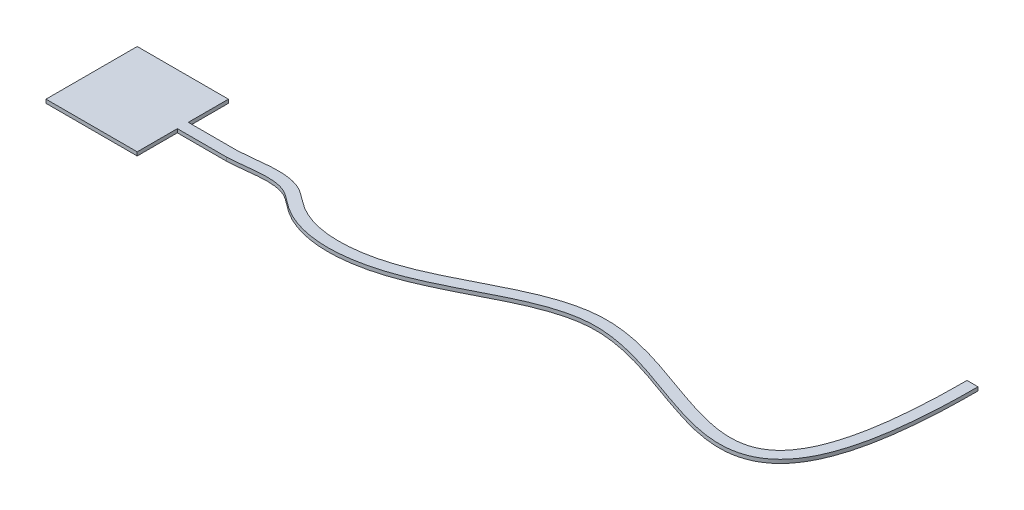
SolidWorks part; units mm, degrees
ref_plane "Front Plane" through (0, 0, 0) normal (0, 0, 1) x (1, 0, 0)
ref_plane "Top Plane" through (0, 0, 0) normal (0, 1, 0) x (1, 0, 0)
ref_plane "Right Plane" through (0, 0, 0) normal (1, 0, 0) x (0, 0, -1)
sketch "Sketch1" plane through (0, 0, 0) normal (0, 1, 0) x (1, 0, 0)
  line L1 (-159.8639, 116.4966) -> (90.1361, 116.4966)
  line L2 (-159.8639, 116.4966) -> (-159.8639, -133.5034)
  line L3 (-159.8639, -133.5034) -> (90.1361, -133.5034)
  line L4 (90.1361, 116.4966) -> (90.1361, -133.5034)
  dimension "D1" = 250
  dimension "D2" = 250
extrude "Boss-Extrude1" add sketch "Sketch1" along normal blind 10
sketch "Sketch2" plane through (0, 10, 0) normal (0, 1, 0) x (1, 0, 0)
  line L0 (90.1361, 116.4966) -> (-159.8639, -133.5034) construction
  line L1 (-159.8639, 116.4966) -> (-159.8639, -133.5034) construction
  line L2 (-159.8639, 116.4966) -> (90.1361, -133.5034) construction
  line L3 (90.1361, 6.4966) -> (90.1361, -23.5034)
  line L4 (1785.1361, 461.0452) -> (1800.1361, 461.0452)
  line L8 (90.1361, -23.5034) -> (224.5985, -23.5034)
  line L9 (90.1361, 6.4966) -> (224.0514, 6.4966)
  line L10 (1785.1361, 461.0452) -> (1770.1361, 461.0452)
  spline S2 degree 3 poles (224.5985, -23.5034) (224.908, -23.4922) (225.5226, -23.4698) (226.7878, -23.419) (228.9875, -23.3209) (233.4066, -23.0851) (242.2645, -22.4728) (254.982, -21.2788) (270.2563, -19.5904) (290.5175, -17.3215) (315.389, -15.0436) (338.8326, -14.9892) (356.2104, -17.0291) (368.4432, -19.7435) (377.9563, -23.1246) (385.0989, -26.5469) (392.1865, -30.6076) (401.3147, -36.9117) (412.7469, -45.7442) (422.9089, -53.527) (431.6523, -59.5736) (440.5529, -65.2298) (452.001, -71.6499) (470.9075, -80.5498) (495.5123, -89.2063) (526.1719, -95.9551) (557.5929, -99.3879) (589.4283, -99.8152) (631.9947, -96.7756) (684.568, -86.9) (744.2911, -67.568) (801.3603, -43.1962) (856.3224, -16.1061) (909.7596, 11.4274) (962.1896, 37.174) (1014.079, 58.9505) (1057.2245, 72.0427) (1091.9375, 78.5028) (1113.7809, 80.6772) (1131.4106, 81.1724) (1149.2625, 80.8598) (1171.9253, 79.0433) (1199.6038, 74.8439) (1237.0165, 66.9225) (1284.4839, 53.3806) (1341.7849, 33.6899) (1398.7165, 13.0067) (1454.6542, -6.195) (1509.0784, -21.408) (1561.5995, -30.0255) (1611.9257, -29.1774) (1651.4323, -17.73) (1680.5206, -0.6421) (1707.5138, 21.9705) (1730.9359, 53.0903) (1750.6053, 93.3966) (1763.5069, 128.508) (1774.5489, 168.8086) (1782.1817, 206.9939) (1787.3253, 240.4712) (1790.695, 267.0859) (1793.5695, 295.2491) (1795.9411, 325.0026) (1797.4914, 351.1569) (1798.4717, 372.917) (1799.0758, 389.6603) (1799.5478, 406.8328) (1799.8863, 424.4363) (1800.0564, 439.4798) (1800.1247, 451.7179) (1800.1361, 457.9451) (1800.1361, 461.0452) knots -0.000148 -0.000148 -0.000148 -0.000148 0.00034 0.000829 0.001805 0.003759 0.007666 0.015479 0.023293 0.031106 0.046734 0.062361 0.070175 0.077988 0.085802 0.089709 0.093616 0.101429 0.109243 0.117057 0.120964 0.12487 0.132684 0.140498 0.156125 0.171752 0.18738 0.203007 0.218634 0.249889 0.281144 0.312398 0.343653 0.374907 0.406162 0.437417 0.468671 0.484299 0.499926 0.50774 0.515553 0.531181 0.546808 0.562435 0.59369 0.624944 0.656199 0.687454 0.718708 0.749963 0.781218 0.812472 0.8281 0.843727 0.874981 0.890609 0.906236 0.921863 0.937491 0.945304 0.953118 0.960932 0.968745 0.976559 0.980466 0.984373 0.98828 0.992186 0.996093 0.998047 1 1 1 1
  spline S4 degree 3 poles (224.0514, 6.4966) (225.1899, 6.539) (227.455, 6.6377) (232.0738, 6.8918) (237.9435, 7.3054) (245.1433, 7.9297) (254.9216, 8.8955) (267.4416, 10.2828) (282.8202, 12.0016) (298.4474, 13.5318) (314.2278, 14.6217) (330.0755, 15.0084) (345.9106, 14.4118) (361.6442, 12.5323) (377.1774, 9.0378) (389.7863, 4.5184) (399.6286, -0.2643) (408.9862, -5.6985) (419.715, -13.2007) (431.6522, -22.4489) (441.1438, -29.6816) (448.6036, -34.807) (456.2683, -39.6528) (466.1382, -45.1561) (482.5447, -52.8357) (504.1136, -60.3843) (531.418, -66.3547) (559.8178, -69.4213) (588.9619, -69.7797) (618.4793, -67.6397) (648.009, -63.2247) (677.1292, -56.7723) (705.683, -48.5134) (743.1603, -35.4299) (789.0258, -15.8299) (843.0012, 10.7772) (896.4258, 38.3044) (949.8657, 64.5442) (1003.9396, 87.2399) (1050.0827, 101.2498) (1087.9269, 108.2708) (1116.8505, 111.1334) (1146.2396, 111.2247) (1175.7233, 108.8266) (1205.2958, 104.3174) (1244.7324, 95.941) (1293.8966, 81.8793) (1352.1526, 61.8428) (1409.0695, 41.1649) (1463.963, 22.3401) (1516.0442, 7.83) (1564.3941, -0.0037) (1607.9968, 0.9366) (1639.8914, 10.3206) (1663.1451, 23.9868) (1679.6075, 37.763) (1695.1245, 55.5595) (1709.6142, 77.8626) (1722.9218, 105.0878) (1734.876, 137.5851) (1745.3177, 175.6635) (1752.6427, 212.2877) (1757.6162, 244.6647) (1760.8894, 270.5218) (1763.6924, 297.9889) (1766.0125, 327.102) (1767.5335, 352.7646) (1768.4968, 374.1541) (1769.0911, 390.6302) (1769.5559, 407.5458) (1769.8896, 424.902) (1770.0574, 439.7473) (1770.1248, 451.8309) (1770.1361, 457.983) (1770.1361, 461.0452) knots 0.000154 0.000154 0.000154 0.000154 0.002107 0.00406 0.007966 0.011871 0.015777 0.023588 0.031399 0.039211 0.047022 0.054833 0.062645 0.070456 0.078267 0.086079 0.089984 0.09389 0.101701 0.109512 0.117324 0.121229 0.125135 0.132946 0.140758 0.15638 0.172003 0.187625 0.203248 0.218871 0.234493 0.250116 0.265738 0.281361 0.312606 0.343851 0.375096 0.406342 0.437587 0.468832 0.484455 0.500077 0.5157 0.531322 0.546945 0.562567 0.593813 0.625058 0.656303 0.687548 0.718793 0.750039 0.781284 0.812529 0.828152 0.843774 0.859397 0.875019 0.890642 0.906264 0.921887 0.93751 0.945321 0.953132 0.960944 0.968755 0.976566 0.980472 0.984377 0.988283 0.992189 0.996094 0.998047 1 1 1 1
  dimension "D1" = 1680
extrude "Boss-Extrude2" add sketch "Sketch2" against normal blind 10
